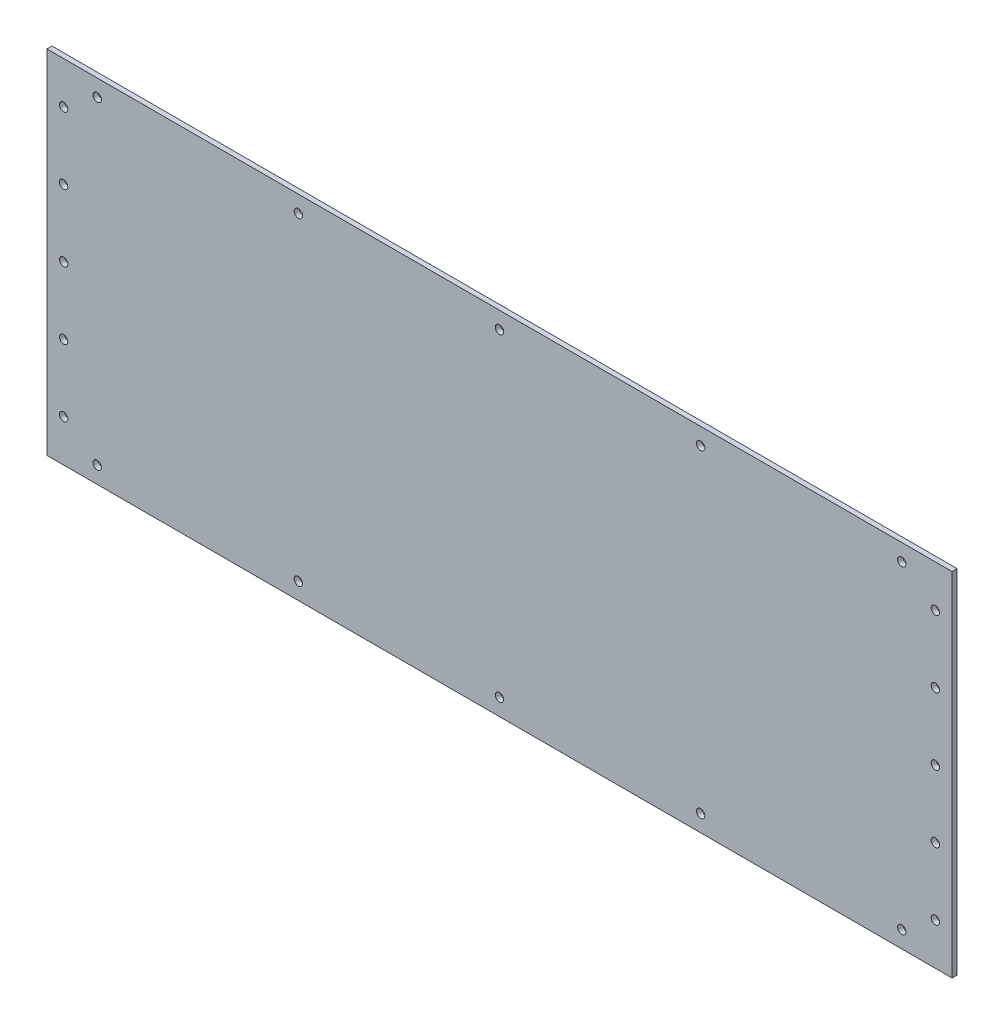
SolidWorks part; units mm, degrees
ref_plane "Alzado" through (0, 0, 0) normal (0, 0, 1) x (1, 0, 0)
ref_plane "Planta" through (0, 0, 0) normal (0, 1, 0) x (1, 0, 0)
ref_plane "Vista lateral" through (0, 0, 0) normal (1, 0, 0) x (0, 0, -1)
sketch "Croquis1" plane through (0, 0, 0) normal (0, 0, 1) x (1, 0, 0)
  line L1 (-270, 105) -> (270, 105)
  line L2 (-270, 105) -> (-270, -105)
  line L3 (-270, -105) -> (270, -105)
  line L4 (270, 105) -> (270, -105)
  line L5 (-270, 105) -> (270, -105) construction
  line L6 (-270, -105) -> (270, 105) construction
  point P0 (0, 0)
  dimension "D1" = 540
  dimension "D2" = 210
extrude "Saliente-Extruir1" add sketch "Croquis1" along normal blind 3
sketch "Croquis2" plane through (0, 0, 3) normal (0, 0, 1) x (1, 0, 0)
  line L0 (-270, 105) -> (-270, -105) construction
  line L1 (-260, -95) -> (260, -95) construction
  line L2 (-260, -95) -> (-260, 95) construction
  line L3 (-260, 95) -> (260, 95) construction
  line L4 (260, -95) -> (260, 95) construction
  line L5 (-260, -95) -> (260, 95) construction
  line L6 (-260, 95) -> (260, -95) construction
  line L7 (270, 105) -> (-270, 105) construction
  line L8 (-270, 0) -> (270, 0) construction
  line L9 (270, -105) -> (270, 105) construction
  line L10 (0, 105) -> (0, -95) construction
  circle A0 centre (0, 95) radius 2.5
  circle A1 centre (-260, 0) radius 2.5
  circle A2 centre (0, -95) radius 2.5
  circle A3 centre (260, 0) radius 2.5
  circle A4 centre (120, 95) radius 2.5
  circle A5 centre (240, 95) radius 2.5
  circle A6 centre (-120, 95) radius 2.5
  circle A7 centre (-240, 95) radius 2.5
  circle A9 centre (-260, -40) radius 2.5
  circle A11 centre (-260, -80) radius 2.5
  circle A12 centre (-260, 40) radius 2.5
  circle A13 centre (-260, 80) radius 2.5
  circle A14 centre (120, -95) radius 2.5
  circle A15 centre (240, -95) radius 2.5
  circle A16 centre (-120, -95) radius 2.5
  circle A17 centre (-240, -95) radius 2.5
  circle A18 centre (260, 40) radius 2.5
  circle A19 centre (260, 80) radius 2.5
  circle A20 centre (260, -40) radius 2.5
  circle A21 centre (260, -80) radius 2.5
  circle A22 centre (0, 15) radius 2.5 [skipped]
  circle A23 centre (0, 55) radius 2.5 [skipped]
  point P0 (0, 0)
  dimension "D3" = 5
  dimension "D1" = 10
  dimension "D2" = 10
  dimension "D4" = 3
  dimension "D5" = 3
  dimension "D6" = 3
  dimension "D7" = 3
  dimension "D8" = 3
  dimension "D9" = 3
  dimension "D10" = 3
  dimension "D11" = 3
extrude "Cortar-Extruir2" cut sketch "Croquis2" against normal through all
